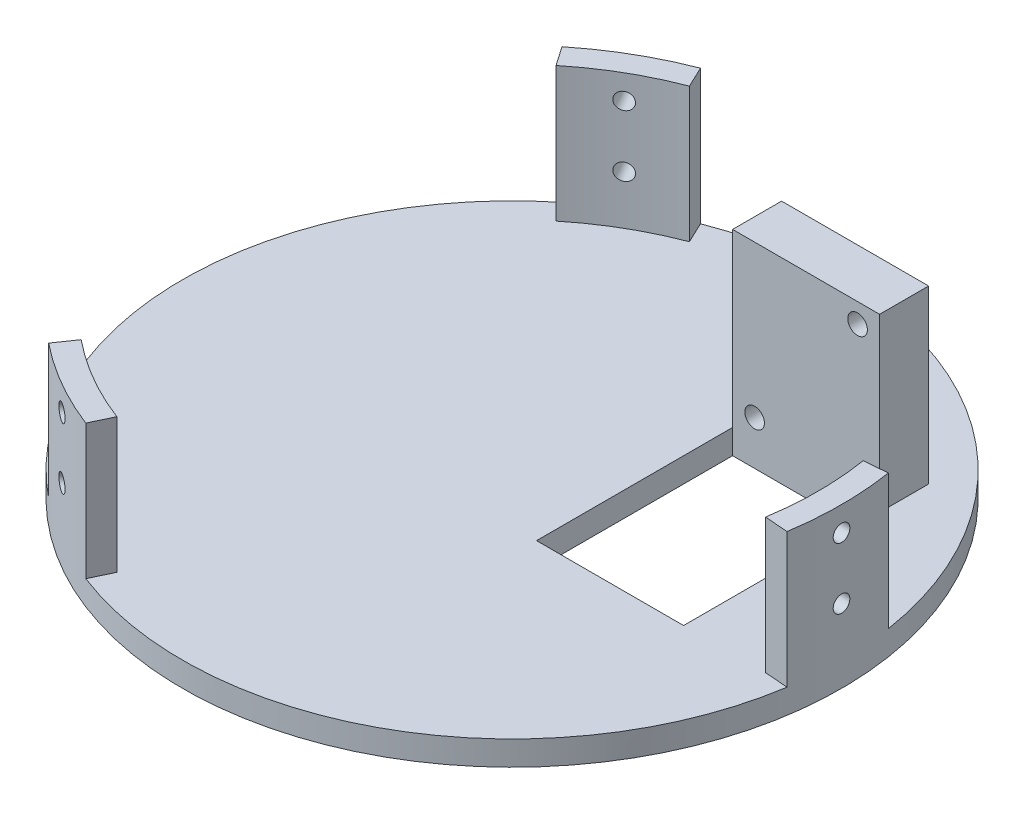
SolidWorks part; units mm, degrees
material "6061-T6 (SS)"
ref_plane "Front" through (0, 0, 0) normal (0, 0, 1) x (1, 0, 0)
ref_plane "Top" through (0, 0, 0) normal (0, 1, 0) x (1, 0, 0)
ref_plane "Right" through (0, 0, 0) normal (1, 0, 0) x (0, 0, -1)
sketch "Sketch1" plane through (0, 0, 0) normal (0, 1, 0) x (1, 0, 0)
  line L1 (0, 0) -> (127.635, 0)
  line L2 (0, 0) -> (0, 127.635)
  line L3 (0, 127.635) -> (127.635, 127.635)
  line L4 (127.635, 0) -> (127.635, 127.635)
  dimension "D1" = 127.635
  dimension "D2" = 127.635
extrude "Main Plate" add sketch "Sketch1" along normal blind 6.35
sketch "Sketch9" plane through (0, 6.35, 0) normal (0, 1, 0) x (1, 0, 0)
  circle A0 centre (63.8175, 63.8175) radius 85.725
  dimension "D1" = 171.45
extrude "Boss-Extrude1" add sketch "Sketch9" against normal up to surface (6.35 mm away) contours A0 up to face at (63.8175, 0, -63.8175)
sketch "Sketch10" plane through (0, 6.35, 0) normal (0, 1, 0) x (1, 0, 0)
  circle A0 centre (63.8175, 63.8175) radius 95.25
  circle A1 centre (63.8175, 63.8175) radius 85.4075
  dimension "D1" = 170.815
  dimension "D2" = 190.5
extrude "Cut-Extrude1" cut sketch "Sketch10" against normal blind 167.64 contours A0 | A1
sketch "Sketch14" plane through (0, 6.35, 0) normal (0, 1, 0) x (1, 0, 0)
  line L0 (201.1692, 63.8175) -> (-73.4523, 63.8175) construction
ref_plane "Plane1" through (0, 0, -63.8175) normal (0, 0, -1) x (-1, 0, 0)
ref_plane "Plane3" through (0, 3.175, 0) normal (0, 1, 0) x (1, 0, 0)
ref_plane "Plane2" through (-21.59, 0, 0) normal (-1, 0, 0) x (0, 0, 1)
sketch "Sketch18" plane through (0, 3.175, 0) normal (0, 1, 0) x (1, 0, 0)
  circle A0 centre (63.8175, 63.8175) radius 85.4075
  circle A1 centre (63.8175, 63.8175) radius 79.375
  circle A4 centre (63.8175, 63.8175) radius 85.4075 construction
  dimension "D1" = 158.75
extrude "Boss-Extrude2" add sketch "Sketch18" along normal blind 38.1
sketch "Sketch20" plane through (0, 6.35, 0) normal (0, 1, 0) x (1, 0, 0)
  line L0 (63.8175, 143.1925) -> (63.8175, -15.5575) construction
  line L1 (-15.5575, 63.8175) -> (143.1925, 63.8175) construction
  line L2 (63.8175, 63.8175) -> (-15.5575, -73.664) construction
  circle A0 centre (63.8175, 63.8175) radius 79.375 construction
  dimension "D1" = 30
ref_plane "Plane5" through (-15.5575, 6.35, 73.664) normal (-0.5, 0, 0.866) x (0.866, 0, 0.5)
sketch "Sketch15" plane through (166.2216, -6.35, 178.6143) normal (0.5, 0, -0.866) x (-0.866, 0, -0.5)
  line L3 (289.2754, 47.625) -> (130.5254, 47.625) construction
  circle A0 centre (209.9004, 25.4) radius 2.159
  circle A1 centre (209.9004, 41.275) radius 2.159
  dimension "D1" = 4.318
  dimension "D2" = 15.875
  dimension "D3" = 4.318
  dimension "D6" = 6.35
extrude "Cut-Extrude3" cut sketch "Sketch15" along normal blind 88.9
pattern_circular "CirPattern1" count 3 over 360 about axis through (63.8175, -161.29, -63.8175) along (0, 1, 0) of "Cut-Extrude3"
ref_plane "Plane4" through (63.8175, 0, 0) normal (-1, 0, 0) x (0, 0, 1)
sketch "Sketch23" plane through (0, 6.35, 0) normal (0, 1, 0) x (1, 0, 0)
  line L0 (13.6787, 125.352) -> (7.5523, 134.2379)
  line L1 (15.1867, 11.8815) -> (13.6787, 2.283) construction
  line L3 (-15.5575, 63.8175) -> (143.1925, 63.8175) construction
  line L4 (63.8175, 143.1925) -> (63.8175, -15.5575) construction
  line L5 (-15.5575, 63.8175) -> (143.1925, 63.8175)
  line L6 (63.8175, 143.1925) -> (63.8175, -15.5575)
  line L7 (13.6787, 2.283) -> (6.9592, -7.4631)
  line L8 (-19.2671, 125.3206) -> (-48.797, 60.3978)
  line L9 (-48.797, 60.3978) -> (-9.8843, 7.0525)
  line L10 (-9.8843, 7.0525) -> (6.9592, -7.4631)
  line L11 (24.1345, -4.9259) -> (13.6787, 2.283) construction
  line L14 (7.5523, 134.2379) -> (-19.2671, 125.3206)
  line L15 (24.1345, 132.5609) -> (13.6787, 125.352) construction
  line L28 (63.8175, 63.8175) -> (24.1345, -4.9259) construction
  line L29 (63.8175, 63.8175) -> (24.1345, 132.5609) construction
  line L30 (142.1773, 76.4717) -> (152.9359, 77.3344)
  line L31 (152.9359, 77.3344) -> (158.6231, 105.0193)
  line L32 (158.6231, 105.0193) -> (117.1632, 163.0543)
  line L33 (117.1632, 163.0543) -> (51.5085, 156.0277)
  line L34 (51.5085, 156.0277) -> (30.5159, 148.6985)
  line L35 (35.5964, 138.0062) -> (30.5159, 148.6985)
  line L36 (35.5964, -10.3712) -> (30.9643, -20.1198)
  line L37 (30.9643, -20.1198) -> (52.0965, -38.8874)
  line L38 (52.0965, -38.8874) -> (123.0863, -31.9996)
  line L39 (123.0863, -31.9996) -> (149.8284, 28.3723)
  line L40 (149.8284, 28.3723) -> (153.9775, 50.217)
  line L41 (142.1773, 51.1633) -> (153.9775, 50.217)
  circle A0 centre (63.8175, 63.8175) radius 79.375 construction
  arc A1 (13.6787, 2.283) -> (13.6787, 125.352) centre (63.8175, 63.8175) cw
  circle A3 centre (63.8175, 63.8175) radius 79.375
  arc A6 (35.5964, 138.0062) -> (142.1773, 76.4717) centre (63.8175, 63.8175) cw
  arc A7 (142.1773, 51.1633) -> (35.5964, -10.3712) centre (63.8175, 63.8175) cw
  circle A9 centre (63.8175, 63.8175) radius 79.375
  dimension "D1" = 79.375
  dimension "D2" = 0
  dimension "D3" = 12.7
  dimension "D4" = 90
  dimension "D5" = 12.7
  dimension "D6" = 90
  dimension "D8" = 60.004
  dimension "D9" = 60.004
  dimension "D7" = 3
extrude "Cut-Extrude6" cut sketch "Sketch23" along normal blind 111.6
sketch "Sketch24" plane through (0, 6.35, 0) normal (0, 1, 0) x (1, 0, 0)
  line L1 (82.8675, 101.9175) -> (120.9675, 101.9175)
  line L2 (82.8675, 101.9175) -> (82.8675, 51.1175)
  line L3 (82.8675, 51.1175) -> (120.9675, 51.1175)
  line L4 (120.9675, 101.9175) -> (120.9675, 51.1175)
  line L5 (82.8675, 101.9175) -> (120.9675, 51.1175) construction
  line L6 (82.8675, 51.1175) -> (120.9675, 101.9175) construction
  arc A0 (148.2085, 76.9553) -> (32.9997, 143.4712) centre (63.8175, 63.8175) ccw construction
  arc A1 (148.2085, 76.9553) -> (32.9997, 143.4712) centre (63.8175, 63.8175) ccw
  point P0 (101.9175, 76.5175)
  dimension "D1" = 50.8
  dimension "D2" = 38.1
  dimension "D3" = 12.7
  dimension "D4" = 38.1
extrude "Cut-Extrude7" cut sketch "Sketch24" against normal through all contours L4 L1 L2 L3
sketch "Sketch25" plane through (0, 6.35, 0) normal (0, 1, 0) x (1, 0, 0)
  line L1 (82.8675, 114.6175) -> (120.9675, 114.6175)
  line L2 (82.8675, 114.6175) -> (82.8675, 101.9175)
  line L3 (82.8675, 101.9175) -> (120.9675, 101.9175)
  line L4 (120.9675, 114.6175) -> (120.9675, 101.9175)
  line L5 (82.8675, 114.6175) -> (120.9675, 101.9175) construction
  line L6 (82.8675, 101.9175) -> (120.9675, 114.6175) construction
  point P0 (101.9175, 108.2675)
  dimension "D1" = 12.7
extrude "Boss-Extrude3" add sketch "Sketch25" along normal blind 44.45
sketch "Sketch26" plane through (0, 0, -101.9175) normal (0, 0, 1) x (1, 0, 0)
  line L1 (82.8675, 50.8) -> (120.9675, 50.8) construction
  line L2 (120.9675, 50.8) -> (120.9675, 6.35) construction
  circle A0 centre (115.2525, 45.72) radius 2.54
  circle A1 centre (88.5825, 11.43) radius 2.54
  dimension "D1" = 5.08
  dimension "D2" = 5.715
  dimension "D3" = 34.29
  dimension "D4" = 5.08
  dimension "D5" = 26.67
extrude "Cut-Extrude8" cut sketch "Sketch26" against normal blind 44.45
